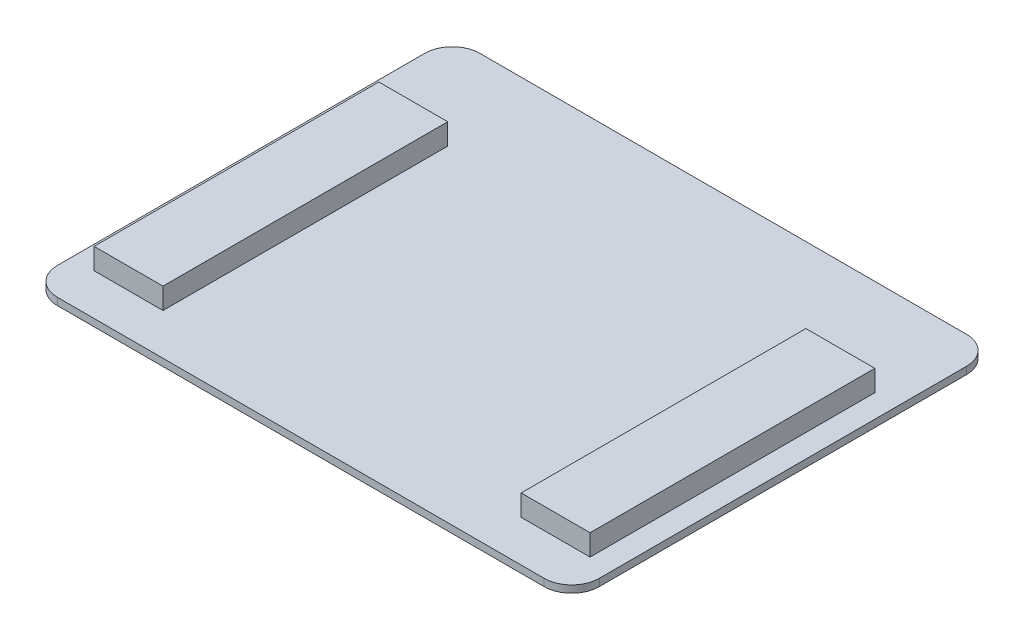
SolidWorks part; units mm, degrees
ref_plane "Front Plane" through (0, 0, 0) normal (0, 0, 1) x (1, 0, 0)
ref_plane "Top Plane" through (0, 0, 0) normal (0, 1, 0) x (1, 0, 0)
ref_plane "Right Plane" through (0, 0, 0) normal (1, 0, 0) x (0, 0, -1)
sketch "Sketch1" plane through (0, 0, 0) normal (0, 1, 0) x (1, 0, 0)
  line L1 (74.93, 58.42) -> (-74.93, 58.42)
  line L2 (74.93, 58.42) -> (74.93, -58.42)
  line L3 (74.93, -58.42) -> (-74.93, -58.42)
  line L4 (-74.93, 58.42) -> (-74.93, -58.42)
  line L5 (74.93, 58.42) -> (-74.93, -58.42) construction
  line L6 (74.93, -58.42) -> (-74.93, 58.42) construction
  point P0 (0, 0)
  dimension "D1" = 116.84
  dimension "D2" = 149.86
extrude "Boss-Extrude1" add sketch "Sketch1" along normal blind 2
fillet "Fillet1" radius 7.62 4 edges at (74.93, 1, 58.42) (74.93, 1, -58.42) (-74.93, 1, -58.42) (-74.93, 1, 58.42)
sketch "Sketch2" plane through (0, 2, 0) normal (0, 1, 0) x (1, 0, 0)
  line L0 (74.93, -50.8) -> (74.93, 50.8) construction
  line L1 (68.58, -46.99) -> (49.53, -46.99)
  line L2 (68.58, -46.99) -> (68.58, 31.75)
  line L3 (68.58, 31.75) -> (49.53, 31.75)
  line L4 (49.53, -46.99) -> (49.53, 31.75)
  line L5 (-67.31, -58.42) -> (67.31, -58.42) construction
  dimension "D1" = 19.05
  dimension "D2" = 6.35
  dimension "D3" = 11.43
  dimension "D4" = 78.74
extrude "Boss-Extrude2" add sketch "Sketch2" along normal blind 5.842
mirror "Mirror1" about plane through (0, 0, 0) normal (1, 0, 0) of "Boss-Extrude2"
